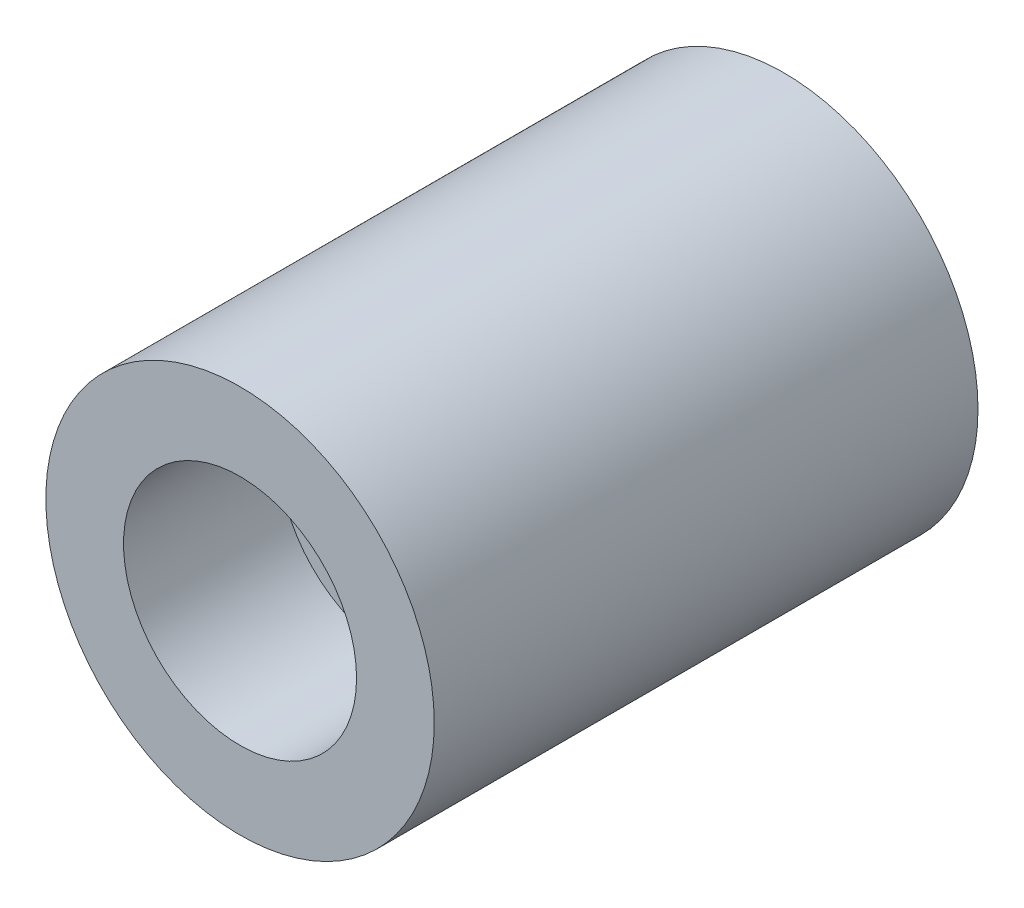
SolidWorks part; units mm, degrees
ref_plane "Front Plane" through (0, 0, 0) normal (0, 0, 1) x (1, 0, 0)
ref_plane "Top Plane" through (0, 0, 0) normal (0, 1, 0) x (1, 0, 0)
ref_plane "Right Plane" through (0, 0, 0) normal (1, 0, 0) x (0, 0, -1)
sketch "Sketch2" plane through (0, 0, 0) normal (0, 0, 1) x (1, 0, 0)
  circle A0 centre (0, 0) radius 50
extrude "Boss-Extrude1" add sketch "Sketch2" along normal blind 140
sketch "Sketch3" plane through (0, 0, 140) normal (0, 0, 1) x (1, 0, 0)
  circle A0 centre (0, 0) radius 30
extrude "Cut-Extrude1" cut sketch "Sketch3" against normal blind 40
sketch "Sketch4" plane through (0, 0, 140) normal (0, 0, 1) x (1, 0, 0)
  circle A0 centre (0, 0) radius 10
extrude "Cut-Extrude2" cut sketch "Sketch4" against normal blind 120
